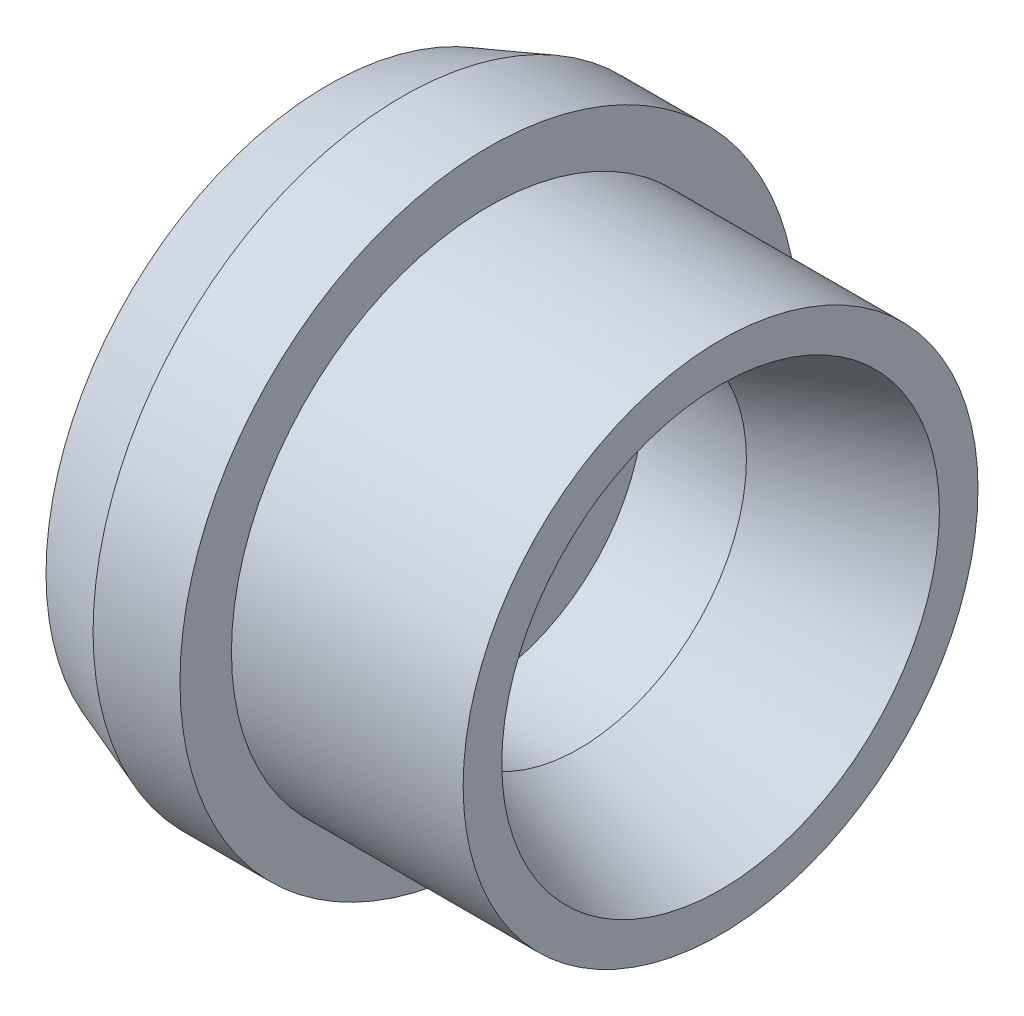
SolidWorks part; units mm, degrees
material "ABS PC"
ref_plane "Front Plane" through (0, 0, 0) normal (0, 0, 1) x (1, 0, 0)
ref_plane "Top Plane" through (0, 0, 0) normal (0, 1, 0) x (1, 0, 0)
ref_plane "Right Plane" through (0, 0, 0) normal (1, 0, 0) x (0, 0, -1)
sketch "Sketch1" plane through (0, 0, 0) normal (0, 0, 1) x (1, 0, 0)
  line L0 (0, 0) -> (0, 5.5644)
  line L1 (0, 5.5644) -> (1.4605, 6.096)
  line L2 (1.4605, 6.096) -> (3.175, 6.096)
  line L3 (3.175, 6.096) -> (3.175, 5.08)
  line L4 (3.175, 5.08) -> (7.747, 5.08)
  line L5 (7.747, 5.08) -> (7.747, 4.318)
  line L7 (2.921, 3.302) -> (2.921, 0)
  line L9 (2.921, 0) -> (0, 0) construction
  line L10 (0, 0) -> (2.921, 0)
  line L11 (2.921, 3.302) -> (4.9556, 3.302)
  line L12 (4.9556, 3.302) -> (7.747, 4.318)
  point P28 (1.4605, 0)
  dimension "D1" = 6.096
  dimension "D2" = 3.175
  dimension "D3" = 4.572
  dimension "D4" = 3.302
  dimension "D5" = 2.921
  dimension "D6" = 20
  dimension "D7" = 5.08
  dimension "D8" = 20
  dimension "D9" = 1.016
revolve "Revolve1" add sketch "Sketch1" angle 360 about L9
move or copy body "Body-Move/Copy1" [suppressed] bodies to move or copy 101 parameters "D1"=0, "D2"=0, "D3"=0
move or copy body "Body-Move/Copy2" [suppressed] bodies to move or copy 102 parameters "D1"=0, "D2"=0, "D3"=0
move or copy body "Body-Move/Copy3" [suppressed] bodies to move or copy 103 parameters "D1"=0, "D2"=0, "D3"=0
move or copy body "Body-Move/Copy4" [suppressed] bodies to move or copy 104 parameters "D1"=0, "D2"=0, "D3"=0
